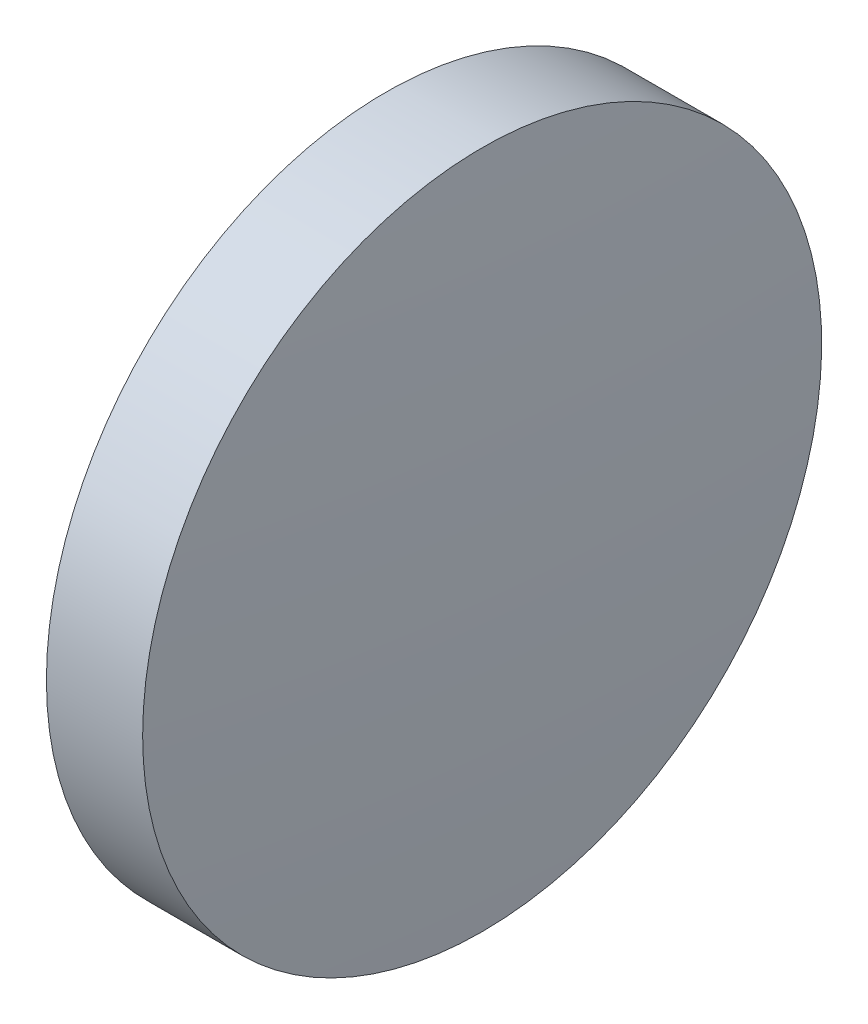
SolidWorks part; units mm, degrees
ref_plane "前视基准面" through (0, 0, 0) normal (0, 0, 1) x (1, 0, 0)
ref_plane "上视基准面" through (0, 0, 0) normal (0, 1, 0) x (1, 0, 0)
ref_plane "右视基准面" through (0, 0, 0) normal (1, 0, 0) x (0, 0, -1)
sketch "草图1" plane through (0, 0, 0) normal (0, 0, 1) x (1, 0, 0)
  line L0 (424.4676, 147.019) -> (443.2636, 147.019) construction
  line L1 (430.0975, 147.019) -> (430.0975, 159.719)
  line L2 (434.0975, 147.019) -> (430.0975, 147.019)
  line L5 (430.0975, 159.719) -> (433.6975, 159.719)
  arc A0 (434.0975, 147.019) -> (433.6975, 159.719) centre (232.285, 147.019) ccw
revolve "旋转1" add sketch "草图1" angle 360 about L0
